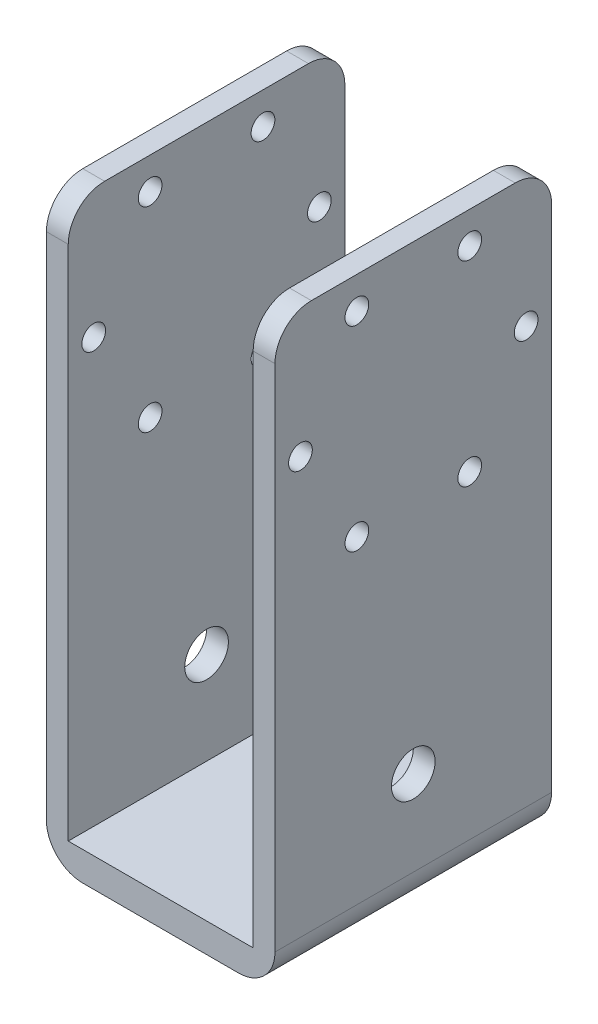
SolidWorks part; units mm, degrees
material "Custom Plastic"
ref_plane "Front Plane" through (0, 0, 0) normal (0, 0, 1) x (1, 0, 0)
ref_plane "Top Plane" through (0, 0, 0) normal (0, 1, 0) x (1, 0, 0)
ref_plane "Right Plane" through (0, 0, 0) normal (1, 0, 0) x (0, 0, -1)
sketch "Sketch1" plane through (0, 0, 0) normal (0, 0, 1) x (1, 0, 0)
  line L0 (-15.7, 80) -> (-12.7, 80)
  line L1 (-12.7, 80) -> (-12.7, 4)
  line L2 (-12.7, 4) -> (12.7, 4)
  line L3 (-15.7, 80) -> (-15.7, 0)
  line L4 (-15.7, 0) -> (15.7, 0)
  line L5 (0, 33.2714) -> (0, -36.0595) construction
  line L6 (15.7, 80) -> (15.7, 0)
  line L7 (12.7, 80) -> (12.7, 4)
  line L8 (15.7, 80) -> (12.7, 80)
  point P11 (0, 0)
  point P13 (0, 4)
  dimension "D1" = 12.7
  dimension "D2" = 4
  dimension "D3" = 3
  dimension "D4" = 80
extrude "Boss-Extrude1" add sketch "Sketch1" along normal mid plane 38
sketch "Sketch2" plane through (15.7, 0, 0) normal (1, 0, 0) x (0, 0, -1)
  line L0 (0, 43.2613) -> (0, -4.7877) construction
  line L1 (-7.75, 75.63) -> (7.75, 75.63) construction
  line L2 (-19, 80) -> (19, 80) construction
  circle A0 centre (-7.75, 75.63) radius 1.63
  circle A1 centre (7.75, 75.63) radius 1.63
  circle A2 centre (-15.5, 62.2) radius 1.63
  circle A3 centre (15.5, 62.2) radius 1.63
  circle A4 centre (-7.75, 48.77) radius 1.63
  circle A5 centre (7.75, 48.77) radius 1.63
  point P7 (0, 75.63)
  dimension "D2" = 3.26
  dimension "D1" = 15.5
  dimension "D3" = 4.37
  dimension "D4" = 13.43
  dimension "D5" = 7.75
  dimension "D6" = 13.43
extrude "Cut-Extrude1" cut sketch "Sketch2" against normal through all
fillet "Fillet1" radius 5 6 edges at (-15.7, 0, 0) (15.7, 0, 0) (-14.2, 80, 19) (-14.2, 80, -19) (14.2, 80, -19) (14.2, 80, 19)
sketch "Sketch3" plane through (0, 4, 0) normal (0, 1, 0) x (1, 0, 0)
  line L0 (0, 25.1826) -> (0, -29.3208) construction
  line L1 (-12, 10) -> (-12, -10) construction
  circle A0 centre (-12, 10) radius 1.5
  circle A1 centre (-12, -10) radius 1.5
  circle A2 centre (12, -10) radius 1.5
  circle A3 centre (12, 10) radius 1.5
  point P4 (-12, 0)
  dimension "D3" = 3
  dimension "D1" = 12
  dimension "D2" = 10
extrude "Cut-Extrude2" [suppressed] cut sketch "Sketch3" against normal through all
sketch "Sketch4" plane through (15.7, 0, 0) normal (1, 0, 0) x (0, 0, -1)
  line L0 (-19, 4) -> (19, 4) construction
  circle A0 centre (0, 16.7) radius 3
  dimension "D1" = 6
  dimension "D2" = 12.7
extrude "Cut-Extrude3" cut sketch "Sketch4" against normal through all
